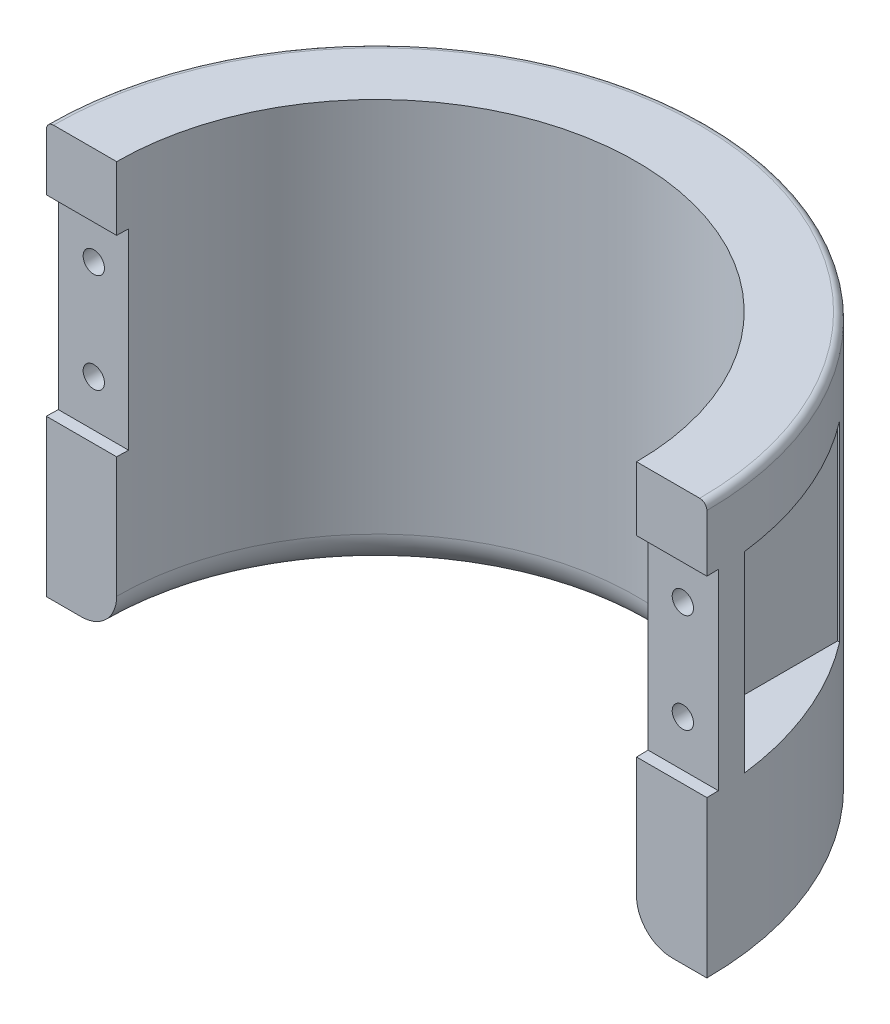
SolidWorks part; units mm, degrees
ref_plane "前视基准面" through (0, 0, 0) normal (0, 0, 1) x (1, 0, 0)
ref_plane "上视基准面" through (0, 0, 0) normal (0, 1, 0) x (1, 0, 0)
ref_plane "右视基准面" through (0, 0, 0) normal (1, 0, 0) x (0, 0, -1)
sketch "草图1" plane through (0, 0, 0) normal (0, 1, 0) x (1, 0, 0)
  line L0 (-46.5, 0) -> (-36.6, 0)
  line L1 (36.6, 0) -> (46.5, 0)
  arc A0 (46.5, 0) -> (-46.5, 0) centre (0, 0) ccw
  arc A1 (36.6, 0) -> (-36.6, 0) centre (0, 0) ccw
  dimension "D1" = 73.2
  dimension "D2" = 93
extrude "凸台-拉伸1" add sketch "草图1" along normal blind 58
fillet "圆角1" radius 5 1 edges at (0, 0, -36.6)
sketch "草图2" plane through (0, 0, 0) normal (0, 0, 1) x (1, 0, 0)
  line L6 (-46.5, 58) -> (-36.6, 58) construction
  line L7 (-48.2491, 22) -> (-34.0507, 22)
  line L8 (-48.2491, 22) -> (-48.2491, 49)
  line L9 (-48.2491, 49) -> (-34.0507, 49)
  line L10 (-34.0507, 22) -> (-34.0507, 49)
  dimension "D1" = 9
  dimension "D2" = 27
extrude "切除-拉伸1" cut sketch "草图2" against normal blind 1.65
sketch "草图3" plane through (0, 0, -1.65) normal (0, 0, 1) x (1, 0, 0)
  line L0 (-46.4707, 22) -> (-46.4707, 49) construction
  line L1 (-46.5, 49) -> (-36.6, 49) construction
  circle A0 centre (-41.4707, 28.5) radius 1.5
  circle A1 centre (-41.4707, 42.5) radius 1.5
  dimension "D1" = 5
  dimension "D2" = 3
  dimension "D5" = 5
  dimension "D3" = 6.5
  dimension "D4" = 14
extrude "切除-拉伸2" cut sketch "草图3" against normal up to next
sketch "草图4" plane through (0, 0, -1.65) normal (0, 0, 1) x (1, 0, 0)
  line L1 (-46.5, 22) -> (-36.6, 22)
  line L2 (-46.5, 22) -> (-46.5, 49)
  line L3 (-46.5, 49) -> (-36.6, 49)
  line L4 (-36.6, 22) -> (-36.6, 49)
ref_plane "基准面1" through (0, 0, -5.65) normal (0, 0, 1) x (1, 0, 0)
sketch "草图5" plane through (0, 0, -5.65) normal (0, 0, 1) x (1, 0, 0)
  line L1 (-46.5, 22) -> (-36.6, 22)
  line L2 (-46.5, 22) -> (-46.5, 49)
  line L3 (-46.5, 49) -> (-36.6, 49)
  line L4 (-36.6, 22) -> (-36.6, 49)
extrude "切除-拉伸3" cut sketch "草图5" against normal blind 22.65
mirror "镜向2" about plane through (0, 0, 0) normal (1, 0, 0) of "切除-拉伸1", "切除-拉伸2", "切除-拉伸3"
fillet "圆角2" radius 1 1 edges at (0, 58, -46.5)
sketch "草图6" plane through (0, 0, 0) normal (0, -1, 0) x (1, 0, 0)
  line L0 (0, 0) -> (0, -54.5695) construction
  circle A0 centre (0, 0) radius 44.5 construction
  circle A1 centre (0, -44.5) radius 1
  circle A2 centre (-42.322, -13.7513) radius 1
  circle A3 centre (-26.1564, 36.0013) radius 1
  circle A4 centre (26.1564, 36.0013) radius 1
  circle A5 centre (42.322, -13.7513) radius 1
  point P17 (0, 0)
  dimension "D1" = 89
  dimension "D2" = 2
  dimension "D3" = 5
sketch "草图7" plane through (0, 0, 0) normal (0, -1, 0) x (1, 0, 0)
  line L0 (0, -41.5) -> (0, -46.5)
  line L1 (-10, -45.412) -> (-10, -40.2772)
  arc A3 (0, -46.5) -> (-10, -45.412) centre (0, 0) cw
  arc A4 (-46.5, 0) -> (46.5, 0) centre (0, 0) ccw construction
  arc A5 (0, -41.5) -> (-10, -40.2772) centre (0, 0) cw
  dimension "D2" = 41.5
  dimension "D1" = 10
sketch "草图8" plane through (0, 0, 0) normal (0, -1, 0) x (1, 0, 0)
  line L0 (0, -41.6) -> (0, -46.5)
  line L1 (-4.3484, -41.3721) -> (-4.8606, -46.2453)
  arc A0 (0, -41.6) -> (-4.3484, -41.3721) centre (0, 0) cw
  arc A1 (-41.6, 0) -> (41.6, 0) centre (0, 0) ccw construction
  arc A2 (0, -46.5) -> (-4.8606, -46.2453) centre (0, 0) cw
  arc A3 (-46.5, 0) -> (46.5, 0) centre (0, 0) ccw construction
  dimension "D1" = 6
extrude "凸台-拉伸2" add sketch "草图8" against normal blind 10
sketch "草图9" plane through (0, 0, 0) normal (0, -1, 0) x (1, 0, 0)
  circle A0 centre (0, 0) radius 44.5 construction
  circle A1 centre (0, -44.5) radius 1
  dimension "D1" = 89
  dimension "D2" = 2
extrude "切除-拉伸4" cut sketch "草图9" against normal blind 2
pattern_circular "阵列(圆周)1" count 5 over 360 about axis through (0, 0, 0) along (0, 1, 0) of "切除-拉伸4"
